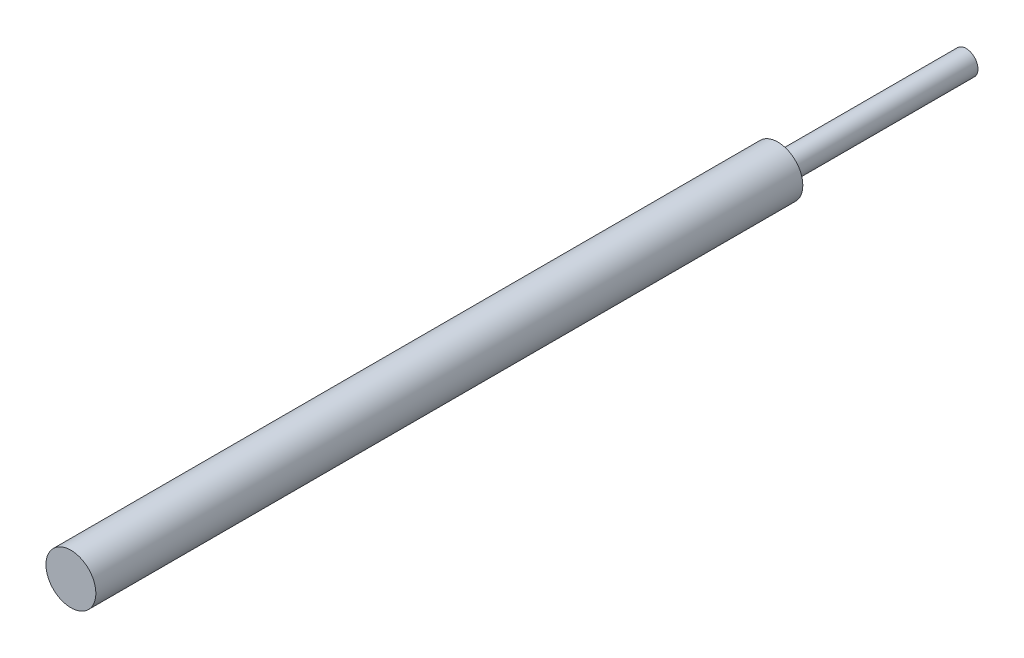
SolidWorks part; units mm, degrees
ref_plane "Front Plane" through (0, 0, 0) normal (0, 0, 1) x (1, 0, 0)
ref_plane "Top Plane" through (0, 0, 0) normal (0, 1, 0) x (1, 0, 0)
ref_plane "Right Plane" through (0, 0, 0) normal (1, 0, 0) x (0, 0, -1)
sketch "Sketch1" plane through (0, 0, 0) normal (0, 0, 1) x (1, 0, 0)
  circle A0 centre (0, 0) radius 2.921
extrude "Extrude1" add sketch "Sketch1" along normal blind 45.974
sketch "Sketch2" plane through (0, 0, 45.974) normal (0, 0, 1) x (1, 0, 0)
  circle A0 centre (0, 0) radius 6.096
extrude "Extrude2" add sketch "Sketch2" along normal blind 172.72
